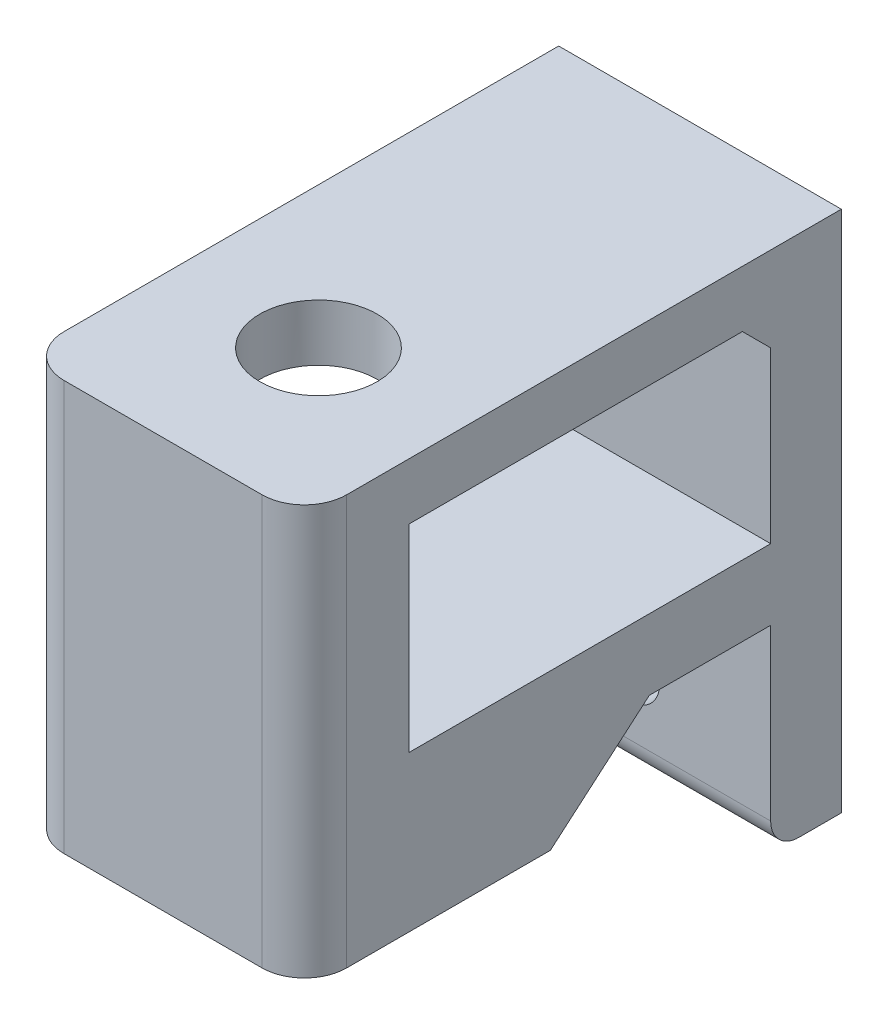
SolidWorks part; units mm, degrees
material "Balsa"
ref_plane "前视基准面" through (0, 0, 0) normal (0, 0, 1) x (1, 0, 0)
ref_plane "上视基准面" through (0, 0, 0) normal (0, 1, 0) x (1, 0, 0)
ref_plane "右视基准面" through (0, 0, 0) normal (1, 0, 0) x (0, 0, -1)
other "Configuration Table"
sketch "Sketch1" plane through (0, 0, 0) normal (0, 0, 1) x (1, 0, 0)
  line L0 (0, -16.5) -> (20, -16.5) construction
  line L1 (0, 0) -> (20, 0)
  line L2 (0, 0) -> (0, -33)
  line L3 (0, -33) -> (20, -33)
  line L4 (20, 0) -> (20, -33)
  circle A0 centre (10, -6.5) radius 2.15
  circle A1 centre (10, -26.5) radius 2.15
  dimension "D3" = 4.3
  dimension "D5" = 20
  dimension "D1" = 20
  dimension "D2" = 33
  dimension "D4" = 10
extrude "Boss-Extrude1" add sketch "Sketch1" along normal blind 5
sketch "Sketch2" plane through (0, 0, 0) normal (0, 0, -1) x (-1, 0, 0)
  line L1 (-20, 0) -> (0, 0)
  line L2 (-20, 0) -> (-20, 4)
  line L3 (-20, 4) -> (0, 4)
  line L4 (0, 0) -> (0, 4)
  dimension "D1" = 4
extrude "Boss-Extrude2" add sketch "Sketch2" against normal blind 38
sketch "Sketch3" plane through (0, 4, 0) normal (0, 1, 0) x (1, 0, 0)
  line L0 (0, 0) -> (20, 0) construction
  circle A0 centre (10, -27) radius 4.15
  point P4 (10, 0)
  dimension "D1" = 27
  dimension "D2" = 8.3
sketch "Sketch4" plane through (0, 0, 0) normal (0, -1, 0) x (1, 0, 0)
  line L0 (20, 38) -> (20, 5) construction
  line L1 (0, 38) -> (20, 38)
  line L2 (0, 38) -> (0, 30.5882)
  line L3 (0, 30.5882) -> (20, 30.5882)
  line L4 (20, 38) -> (20, 30.5882)
extrude "Boss-Extrude3" add sketch "Sketch4" along normal blind 25
fillet "Fillet1" radius 3 2 edges at (0, -10.5, 38) (20, -10.5, 38)
fillet "Fillet2" radius 2 1 edges at (10, -33, 5)
sketch "Sketch5" plane through (20, 0, 0) normal (1, 0, 0) x (0, 0, -1)
  line L0 (-30.5882, 0) -> (-30.5882, -20)
  line L1 (-30.5882, -25) -> (-30.5882, 0) construction
  line L2 (-30.5882, -20) -> (-10.5882, 0)
  line L3 (-30.5882, 0) -> (-5, 0) construction
  line L4 (-10.5882, 0) -> (-30.5882, 0)
  dimension "D1" = 20
  dimension "D2" = 20
chamfer "Chamfer2" distance 2 angle 45 1 edges at (10, 0, 5)
sketch "Sketch8" plane through (0, 0, 5) normal (0, 0, 1) x (1, 0, 0)
  line L0 (0, -2) -> (0, -31) construction
  line L1 (0, -14) -> (20, -14)
  line L2 (0, -14) -> (0, -19)
  line L3 (0, -19) -> (20, -19)
  line L4 (20, -14) -> (20, -19)
  line L5 (20, -31) -> (20, -2) construction
  circle A2 centre (10, -6.5) radius 2.15 construction
  dimension "D1" = 12.5
  dimension "D2" = 5
extrude "Boss-Extrude5" add sketch "Sketch8" along normal up to surface (25.5882 mm away) contours L2 L1 L4 L3 up to face at (10, -12.5, 30.5882)
ref_plane "Plane1" through (20, -14, 30.5882) normal (1, 0, 0) x (0, 0, -1)
sketch "Sketch12" plane through (0, -14, 0) normal (0, 1, 0) x (1, 0, 0)
  line L0 (0, -35) -> (0, 0) construction
  line L1 (20, -30.5882) -> (0, -30.5882)
  line L2 (20, -30.5882) -> (20, -20.5882)
  line L3 (20, -20.5882) -> (0, -20.5882)
  line L4 (0, -30.5882) -> (0, -20.5882)
  dimension "D1" = 10
extrude "Boss-Extrude6" add sketch "Sketch12" along normal up to surface (14 mm away) up to face at (10, 0, 18.7941)
extrude "Cut-Extrude2" cut sketch "Sketch3" against normal up to surface (18 mm away) contours A0 up to face at (10, -14, 12.7941)
sketch "Sketch15" plane through (0, 0, 30.5882) normal (0, 0, -1) x (-1, 0, 0)
  line L0 (0, -25) -> (-20, -25) construction
  line L1 (0, -25) -> (0, -19) construction
  line L2 (0, -19) -> (-20, -19) construction
  line L3 (-20, -25) -> (-20, -19) construction
  line L4 (0, -25) -> (-20, -25)
  line L5 (0, -25) -> (0, -19)
  line L6 (0, -19) -> (-20, -19)
  line L7 (-20, -25) -> (-20, -19)
extrude "Boss-Extrude7" add sketch "Sketch15" along normal blind 10
sketch "Sketch16" plane through (0, 0, 20.5882) normal (0, 0, -1) x (-1, 0, 0)
  line L1 (-20, 0) -> (0, 0)
  line L2 (-20, 0) -> (-20, -14)
  line L3 (-20, -14) -> (0, -14)
  line L4 (0, 0) -> (0, -14)
extrude "Cut-Extrude4" cut sketch "Sketch16" against normal blind 10
sketch "Sketch17" plane through (20, 0, 0) normal (1, 0, 0) x (0, 0, -1)
  line L0 (-20.5882, -19) -> (-20.5882, -25)
  line L1 (-20.5882, -25) -> (-13.5882, -19)
  line L2 (-20.5882, -19) -> (-5, -19) construction
  line L3 (-13.5882, -19) -> (-20.5882, -19)
  dimension "D1" = 7
extrude "Boss-Extrude8" add sketch "Sketch17" against normal up to surface (20 mm away) up to face at (0, -6, 15.6353)
